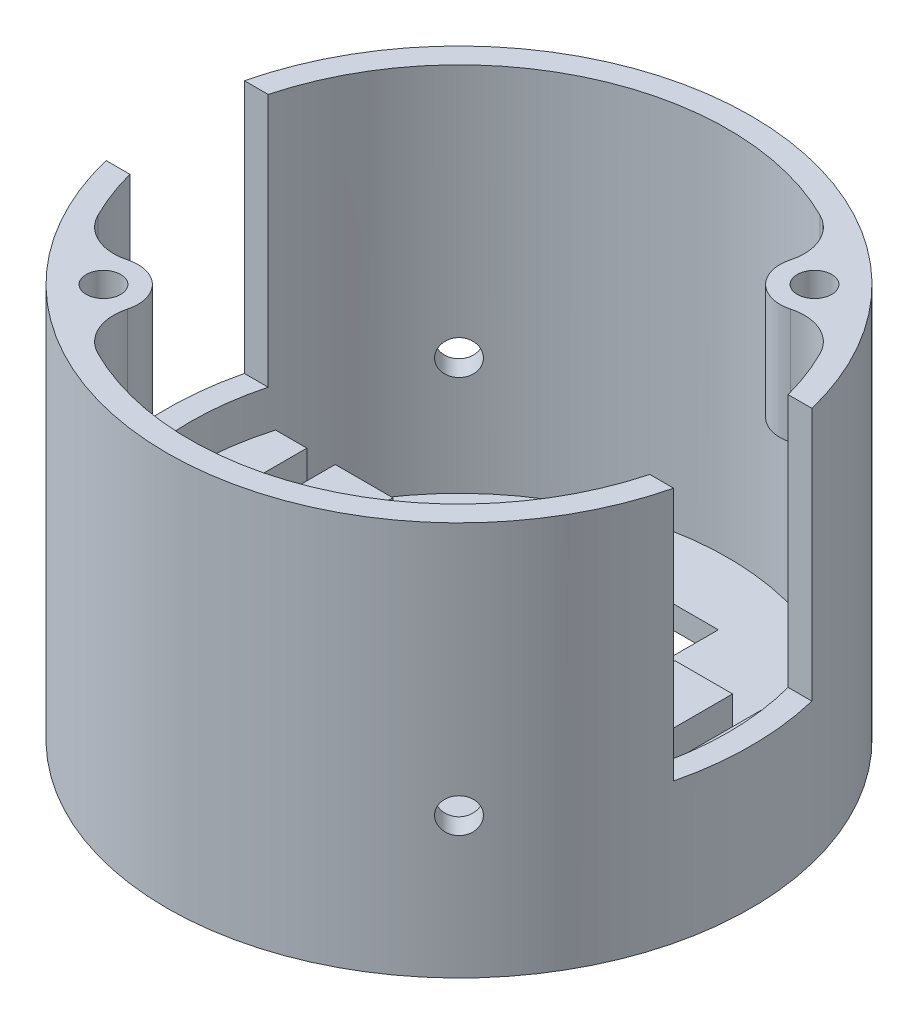
SolidWorks part; units mm, degrees
ref_plane "Front Plane" through (0, 0, 0) normal (0, 0, 1) x (1, 0, 0)
ref_plane "Top Plane" through (0, 0, 0) normal (0, 1, 0) x (1, 0, 0)
ref_plane "Right Plane" through (0, 0, 0) normal (1, 0, 0) x (0, 0, -1)
sketch "Sketch1" plane through (0, 0, 0) normal (0, 1, 0) x (1, 0, 0)
  circle A0 centre (0, 0) radius 25.34
  dimension "D1" = 50.68
extrude "Boss-Extrude1" add sketch "Sketch1" along normal blind 34.2
shell "Shell1" thickness 2
sketch "Sketch2" plane through (0, 34.2, 0) normal (0, 1, 0) x (1, 0, 0)
  line L0 (-42.4931, 0) -> (45.3167, 0) construction
  line L2 (25.34, 6) -> (-25.34, 6)
  line L3 (25.34, 6) -> (25.34, -6)
  line L4 (25.34, -6) -> (-25.34, -6)
  line L5 (-25.34, 6) -> (-25.34, -6)
  line L6 (25.34, 6) -> (-25.34, -6) construction
  line L7 (25.34, -6) -> (-25.34, 6) construction
  circle A0 centre (0, 0) radius 25.34 construction
  point P3 (0, 0)
  dimension "D1" = 12
extrude "Cut-Extrude1" cut sketch "Sketch2" against normal blind 22
sketch "Sketch3" plane through (0, 2, 0) normal (0, 1, 0) x (1, 0, 0)
  line L0 (-17.24, 0) -> (17.24, 0) construction
  line L1 (0, 31.0189) -> (0, -32.0406) construction
  line L2 (17.24, 6.5) -> (12.24, 6.5)
  line L3 (17.24, 6.5) -> (17.24, -6.5)
  line L4 (17.24, -6.5) -> (12.24, -6.5)
  line L5 (12.24, 6.5) -> (12.24, -6.5)
  line L10 (22.4166, 6.5) -> (19.7, 6.5)
  line L11 (19.7, 6.5) -> (19.7, -6.5)
  line L12 (19.7, -6.5) -> (22.4166, -6.5)
  line L13 (-19.7, -6.5) -> (-22.4166, -6.5)
  line L18 (-17.24, -6.5) -> (-12.24, -6.5)
  line L19 (-12.24, 6.5) -> (-12.24, -6.5)
  line L20 (-17.24, 6.5) -> (-12.24, 6.5)
  line L21 (-17.24, 6.5) -> (-17.24, -6.5)
  line L22 (-22.4166, 6.5) -> (-19.7, 6.5)
  line L23 (-19.7, 6.5) -> (-19.7, -6.5)
  arc A0 (22.4166, -6.5) -> (22.4166, 6.5) centre (0, 0) ccw
  circle A2 centre (0, 0) radius 23.34 construction
  arc A3 (-22.4166, 6.5) -> (-22.4166, -6.5) centre (0, 0) ccw
  point P3 (0, 0)
  point P8 (17.24, 0)
  point P26 (0, 0)
  dimension "D1" = 39.4
  dimension "D2" = 13
  dimension "D3" = 5
  dimension "D4" = 2.46
extrude "Boss-Extrude2" add sketch "Sketch3" along normal blind 6.8
sketch "Sketch4" plane through (0, 34.2, 0) normal (0, 1, 0) x (1, 0, 0)
  line L0 (-15.4231, -15.4231) -> (15.4231, 15.4231) construction
  line L1 (-36.246, 0) -> (36.4607, 0) construction
  circle A0 centre (15.4231, 15.4231) radius 3
  circle A1 centre (15.4231, 15.4231) radius 1.5
  circle A2 centre (-15.4231, -15.4231) radius 3
  circle A3 centre (-15.4231, -15.4231) radius 1.5
  point P2 (0, 0)
  dimension "D2" = 3
  dimension "D3" = 6
  dimension "D1" = 45
  dimension "D4" = 43.6232
extrude "Boss-Extrude3" add sketch "Sketch4" against normal blind 10
fillet "Fillet1" radius 4 4 edges at (18.281, 29.2, -14.5107) (14.5107, 29.2, -18.281) (-18.281, 29.2, 14.5107) (-14.5107, 29.2, 18.281)
sketch "Sketch5" plane through (0, 34.2, 0) normal (0, 1, 0) x (1, 0, 0)
  line L0 (-41.8365, 0) -> (43.5087, 0) construction
  line L1 (-17.9181, 17.9181) -> (17.9181, -17.9181) construction
  arc A0 (24.6194, 6) -> (-24.6194, 6) centre (0, 0) ccw construction
  arc A1 (-24.6194, -6) -> (24.6194, -6) centre (0, 0) ccw construction
  dimension "D1" = 45
ref_plane "Plane1" through (17.9181, 34.2, 17.9181) normal (0.7071, 0, 0.7071) x (0.7071, 0, -0.7071)
sketch "Sketch6" plane through (17.9181, 34.2, 17.9181) normal (0.7071, 0, 0.7071) x (0.7071, 0, -0.7071)
  line L1 (-29.5829, 0) -> (30.7653, 0) construction
  circle A0 centre (0, -22) radius 1.5
  dimension "D1" = 3
  dimension "D2" = 22
extrude "Cut-Extrude2" cut sketch "Sketch6" against normal through all
sketch "Sketch7" plane through (0, 2, 0) normal (0, 1, 0) x (1, 0, 0)
  line L0 (-39.6427, 0) -> (42.9579, 0) construction
  line L1 (5, 17.5) -> (-5, 17.5)
  line L2 (5, 17.5) -> (5, 12.5)
  line L3 (5, 12.5) -> (-5, 12.5)
  line L4 (-5, 17.5) -> (-5, 12.5)
  line L5 (5, 17.5) -> (-5, 12.5) construction
  line L6 (5, 12.5) -> (-5, 17.5) construction
  line L7 (5, -12.5) -> (-5, -17.5) construction
  line L8 (5, -17.5) -> (-5, -12.5) construction
  line L9 (5, -12.5) -> (-5, -12.5)
  line L10 (-5, -17.5) -> (-5, -12.5)
  line L11 (5, -17.5) -> (-5, -17.5)
  line L12 (5, -17.5) -> (5, -12.5)
  point P0 (0, 15)
  point P5 (0, -15)
  dimension "D1" = 5
  dimension "D2" = 10
  dimension "D3" = 15
extrude "Cut-Extrude3" cut sketch "Sketch7" against normal through all
